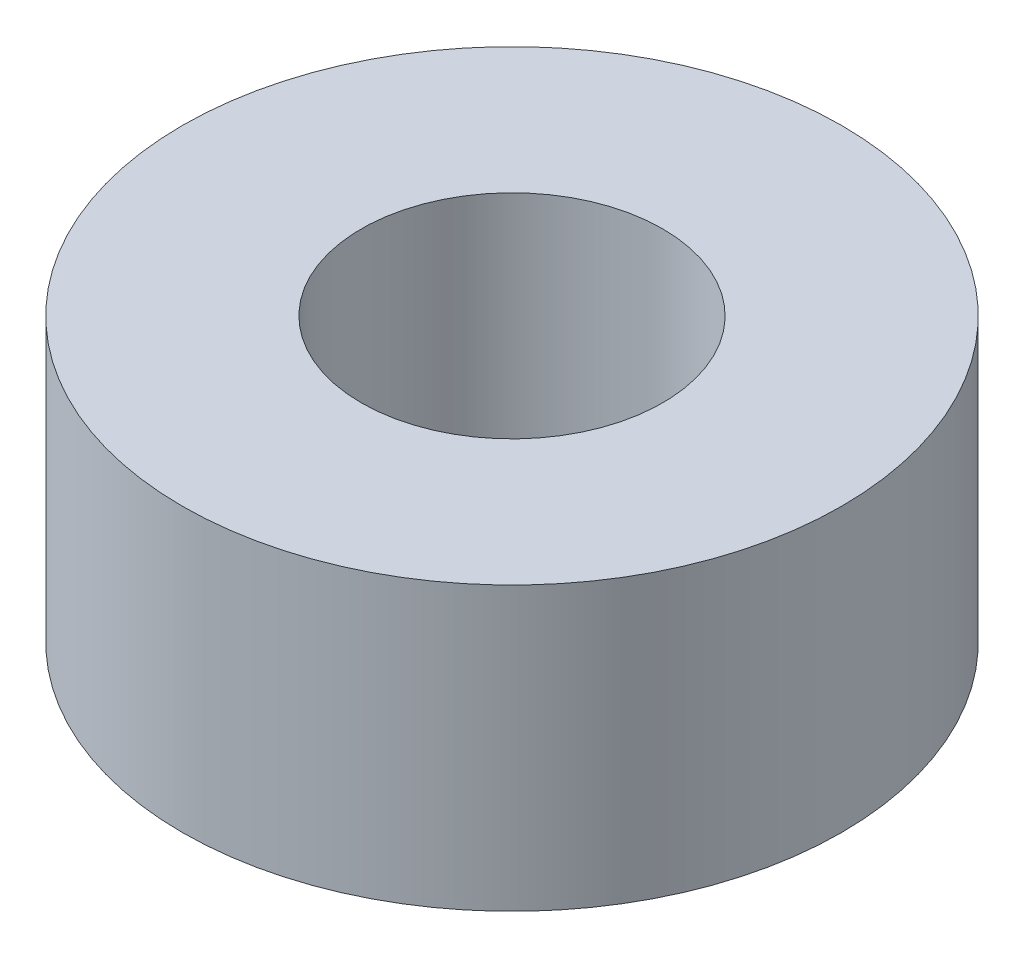
SolidWorks part; units mm, degrees
ref_plane "正面" through (0, 0, 0) normal (0, 0, 1) x (1, 0, 0)
ref_plane "平面" through (0, 0, 0) normal (0, 1, 0) x (1, 0, 0)
ref_plane "右側面" through (0, 0, 0) normal (1, 0, 0) x (0, 0, -1)
sketch "ｽｹｯﾁ1" plane through (0, 0, 0) normal (0, 1, 0) x (1, 0, 0)
  circle A0 centre (0, 0) radius 3.5
extrude "ﾎﾞｽ - 押し出し1" add sketch "ｽｹｯﾁ1" along normal blind 3
sketch "ｽｹｯﾁ2" plane through (0, 3, 0) normal (0, 1, 0) x (1, 0, 0)
  circle A0 centre (0, 0) radius 1.6
extrude "ｶｯﾄ - 押し出し1" cut sketch "ｽｹｯﾁ2" against normal blind 3
